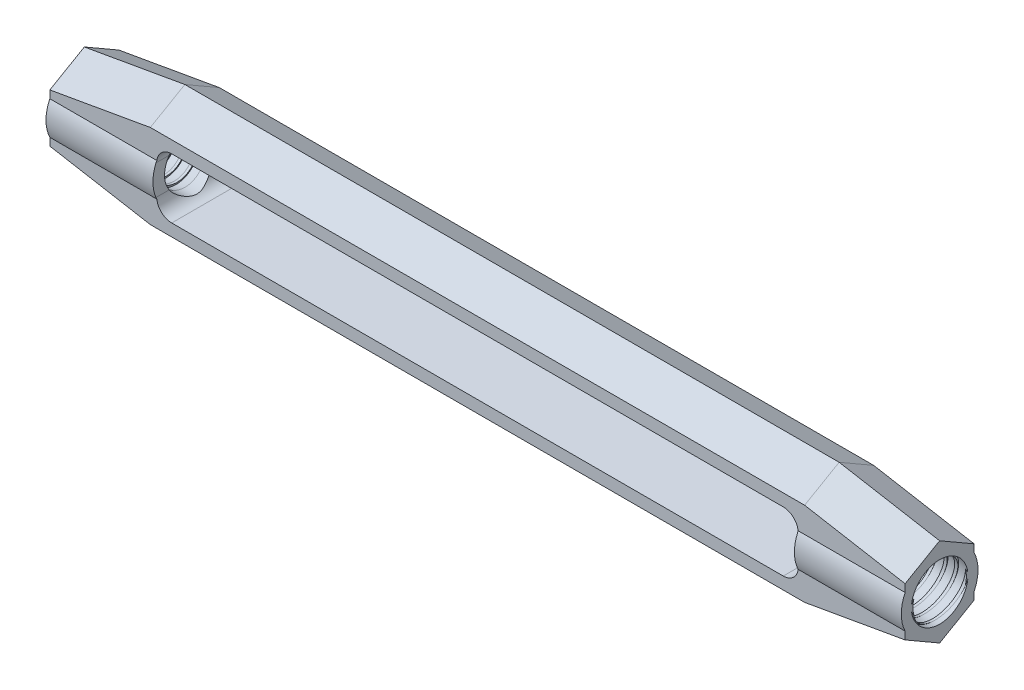
SolidWorks part; units mm, degrees
ref_plane "Front" through (0, 0, 0) normal (0, 0, 1) x (1, 0, 0)
ref_plane "Top" through (0, 0, 0) normal (0, 1, 0) x (1, 0, 0)
ref_plane "Right" through (0, 0, 0) normal (1, 0, 0) x (0, 0, -1)
sketch "Sketch1" plane through (0, 0, 0) normal (1, 0, 0) x (0, 0, -1)
  line L0 (0, 7.366) -> (0, -7.366) construction
  line L1 (0, -7.366) -> (5.207, -4.3597)
  line L2 (5.207, -4.3597) -> (5.207, 4.3597)
  line L3 (5.207, 4.3597) -> (0, 7.366)
  line L4 (0, 7.366) -> (-5.207, 4.3597)
  line L5 (-5.207, 4.3597) -> (-5.207, -4.3597)
  line L6 (-5.207, -4.3597) -> (0, -7.366)
  line L7 (-5.207, 0) -> (5.207, 0) construction
  dimension "D1" = 8.7195
  dimension "Body Width" = 10.414
  dimension "D2" = 120
  dimension "Body Height" = 14.732
extrude "Extrude1" add sketch "Sketch1" along normal mid plane 101.6
sketch "Sketch23" plane through (0, 0, 0) normal (1, 0, 0) x (0, 0, -1)
  line L0 (-4.1005, 7.366) -> (-4.1005, 1.986)
  line L1 (-4.1005, -1.986) -> (-4.1005, -7.366)
  line L2 (-4.1005, -7.366) -> (-5.207, -7.366)
  line L3 (-5.207, -7.366) -> (-5.207, 7.366)
  line L4 (-5.207, 7.366) -> (-4.1005, 7.366)
  line L5 (-5.207, 4.3597) -> (-5.207, -4.3597) construction
  line L6 (0, 3.2281) -> (0, -2.3556) construction
  arc A0 (-4.1005, 1.986) -> (-4.1005, -1.986) centre (0, 0) ccw
  dimension "D2" = 9.1122
  dimension "D1" = 8.201
extrude "Cut-Extrude3" cut sketch "Sketch23" against normal through all and the other way through all
mirror "Mirror2" about plane through (0, 0, 0) normal (0, 0, 1) of "Cut-Extrude3"
sketch "Sketch24" plane through (50.8, 0, 0) normal (1, 0, 0) x (0, 0, -1)
  line L0 (-5.207, 2.2547) -> (0, 5.261)
  line L1 (0, 5.261) -> (5.207, 2.2547)
  line L2 (5.207, 2.2547) -> (5.207, 7.366)
  line L3 (5.207, 7.366) -> (-5.207, 7.366)
  line L4 (-5.207, 7.366) -> (-5.207, 2.2547)
  line L5 (0, 7.366) -> (-5.207, 4.3597) construction
  line L6 (5.207, 4.3597) -> (0, 7.366) construction
  line L7 (-5.207, 4.3597) -> (-5.207, -4.3597) construction
  line L8 (5.207, -4.3597) -> (5.207, 4.3597) construction
  circle A0 centre (0, 0) radius 4.5561 construction
  arc A1 (-4.1005, 1.986) -> (-4.1005, -1.986) centre (0, 0) ccw construction
sketch "Sketch25" plane through (0, 0, 0) normal (0, 0, 1) x (1, 0, 0)
  line L0 (50.8, 5.261) -> (38.8617, 5.261) construction
  line L1 (50.8, 5.261) -> (38.8617, 7.366) construction
  line L2 (50.8, 7.366) -> (-50.8, 7.366) construction
  dimension "D1" = 10
extrude "Cut-Extrude4" cut sketch "Sketch24" along direction (-0.9848, 0.1736, 0) on the side against the normal blind 50.8
mirror "Mirror3" about plane through (0, 0, 0) normal (0, 1, 0) of "Cut-Extrude4"
mirror "Mirror4" about plane through (0, 0, 0) normal (1, 0, 0) of "Mirror3"
sketch "Sketch2" plane through (0, 0, 0) normal (0, 0, 1) x (1, 0, 0)
  line L0 (-38.1, -3.556) -> (38.1, 3.556) construction
  line L1 (-38.1, 3.556) -> (38.1, 3.556)
  line L2 (-38.1, 3.556) -> (-38.1, -3.556)
  line L3 (-38.1, -3.556) -> (38.1, -3.556)
  line L4 (38.1, 3.556) -> (38.1, -3.556)
  line L5 (-50.8, 1.986) -> (-50.8, -1.986) construction
  dimension "D1" = 12.7
  dimension "Take-Up" = 76.2
  dimension "Body ID" = 7.112
extrude "Cut-Extrude1" cut sketch "Sketch2" against normal through all and the other way through all
sketch "Sketch26" plane through (0, 0, 0) normal (1, 0, 0) x (0, 0, -1)
  line L1 (5.207, -4.3597) -> (5.207, 4.3597) construction
  line L2 (0, -7.366) -> (5.207, -4.3597) construction
  line L3 (-5.207, -4.3597) -> (0, -7.366) construction
  line L4 (-5.207, 4.3597) -> (-5.207, -4.3597) construction
  line L5 (0, 7.366) -> (-5.207, 4.3597) construction
  line L6 (5.207, 4.3597) -> (0, 7.366) construction
  line L7 (5.207, -4.3597) -> (5.207, 4.3597)
  line L8 (0, -7.366) -> (5.207, -4.3597)
  line L9 (-5.207, -4.3597) -> (0, -7.366)
  line L10 (-5.207, 4.3597) -> (-5.207, -4.3597)
  line L11 (0, 7.366) -> (-5.207, 4.3597)
  line L12 (5.207, 4.3597) -> (0, 7.366)
extrude "Extrude2" [suppressed] add sketch "Sketch26" along normal mid plane 12.7
sketch "Sketch27" [suppressed] plane through (0, 0, 5.207) normal (0, 0, 1) x (1, 0, 0)
  circle A0 centre (0, 0) radius 1.5875
  dimension "D1" = 3.175
extrude "Cut-Extrude5" [suppressed] cut sketch "Sketch27" against normal through all
fillet "Fillet1" radius 1.778 4 edges at (38.1, 3.556, 0) (38.1, -3.556, 0) (-38.1, -3.556, 0) (-38.1, 3.556, 0)
sketch "Sketch13" plane through (0, 0, 0) normal (0, 0, 1) x (1, 0, 0)
  line L0 (-411.1625, 0) -> (50.8, 0) construction
  line L1 (-50.8, 3.175) -> (50.8, 3.175)
  line L2 (-50.8, 3.175) -> (-50.8, 0)
  line L3 (-50.8, 0) -> (50.8, 0)
  line L4 (50.8, 3.175) -> (50.8, 0)
  line L5 (-50.8, 1.986) -> (-50.8, -1.986) construction
  line L8 (-50.8, -3.175) -> (50.8, -3.175) construction
  line L9 (50.8, -1.986) -> (50.8, 1.986) construction
  dimension "Thread Dia" = 6.35
revolve "Cut-Revolve7" cut sketch "Sketch13" angle 360 about L0
sketch "Sketch22" plane through (0, 0, 0) normal (0, 0, 1) x (1, 0, 0)
  line L0 (52.7985, 3.175) -> (52.7985, -3.175) construction
  line L1 (52.7985, -3.175) -> (51.5285, -3.175) construction
  line L2 (52.7985, 3.175) -> (52.6429, 3.2061) construction
  line L3 (52.6429, 3.2061) -> (51.5532, 3.4241)
  line L4 (51.5532, 3.4241) -> (51.8075, 2.6722)
  line L5 (51.8075, 2.6722) -> (52.1189, 2.6099)
  line L6 (52.1189, 2.6099) -> (52.6429, 3.2061)
  line L7 (51.9632, 2.641) -> (52.098, 3.3151) construction
  line L8 (-50.8, -3.175) -> (50.8, -3.175) construction
  line L11 (52.7985, 3.175) -> (51.5285, -3.175) construction
  line L12 (-50.8, 3.175) -> (50.8, 3.175) construction
  line L15 (52.07, 3.175) -> (50.8, -3.175) construction
  line L16 (50.7345, 0.1401) -> (52.1355, -0.1401) construction
  point P25 (51.435, 0)
  dimension "D1" = 60
  dimension "D2" = 1.27
  dimension "Thread Pitch" = 1.27
  dimension "D4" = 0.1588
  dimension "D5" = 0.3175
revolve "Cut-Revolve8" cut sketch "Sketch22" angle 360 about L16
pattern_linear "LPattern1" count 10 spacing 1.27 along (-1, 0, 0) of "Cut-Revolve8"
mirror "Mirror1" about plane through (0, 0, 0) normal (1, 0, 0) of "LPattern1", "Cut-Revolve8"
equation "\"D1@Fillet1\"=\"Body ID@Sketch2\"/4"
equation "\"D2@Sketch22\"=\"Thread Pitch@Sketch22\""
equation "\"D4@Sketch22\"=\"Thread Pitch@Sketch22\"/8"
equation "\"D5@Sketch22\"=\"Thread Pitch@Sketch22\"/4"
equation "\"D3@LPattern1\"=\"Thread Pitch@Sketch22\""
equation "\"D2@Sketch23\"=\"Body Width@Sketch1\"*7/8"
equation "\"D1@Sketch23\"=\"D2@Sketch23\"*.9"
equation "\"D1@Extrude2\"=\"D1@Sketch2\""
equation "\"D1@Sketch27\"=\"Thread Dia@Sketch13\"/2"
equation "\"D1@LPattern1\"=\"D1@Sketch2\"/\"Thread Pitch@Sketch22\""
